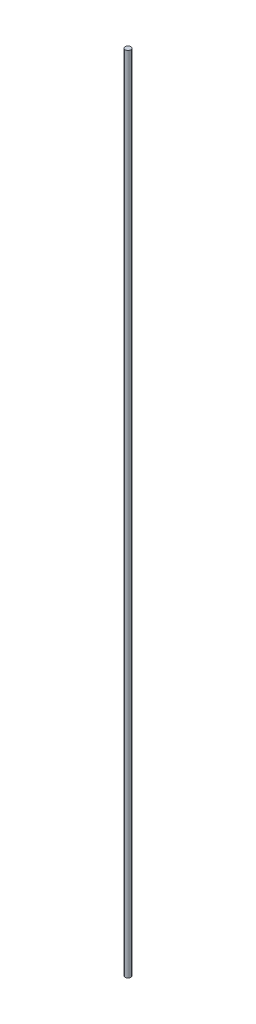
SolidWorks part; units mm, degrees
ref_plane "Front Plane" through (0, 0, 0) normal (0, 0, 1) x (1, 0, 0)
ref_plane "Top Plane" through (0, 0, 0) normal (0, 1, 0) x (1, 0, 0)
ref_plane "Right Plane" through (0, 0, 0) normal (1, 0, 0) x (0, 0, -1)
sketch "Sketch1" plane through (0, 0, 0) normal (0, 1, 0) x (1, 0, 0)
  circle A0 centre (0, 0) radius 2
  dimension "D1" = 4
extrude "Boss-Extrude1" add sketch "Sketch1" along normal blind 588
